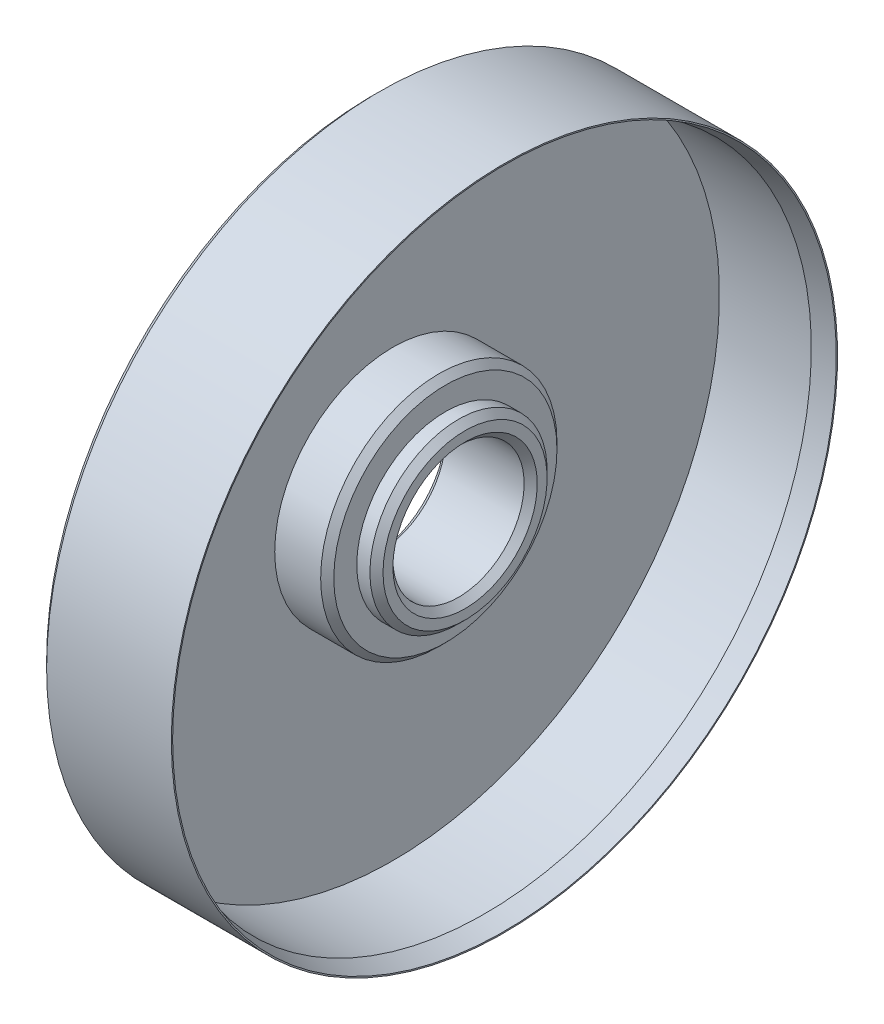
SolidWorks part; units mm, degrees
ref_plane "Спереди" through (0, 0, 0) normal (0, 0, 1) x (1, 0, 0)
ref_plane "Сверху" through (0, 0, 0) normal (0, 1, 0) x (1, 0, 0)
ref_plane "Справа" through (0, 0, 0) normal (1, 0, 0) x (0, 0, -1)
other "Configuration Table"
sketch "Эскиз1" plane through (0, 0, 0) normal (0, 0, 1) x (1, 0, 0)
  line L0 (0, 0) -> (36, 0) construction
  line L1 (0, 11) -> (0, 49.75)
  line L2 (1, 50.75) -> (20, 50.75)
  line L3 (20, 50.75) -> (20, 50.5538)
  line L4 (20, 50.5538) -> (17, 49.75)
  line L5 (17, 49.75) -> (3, 49.75)
  line L6 (3, 49.75) -> (3, 18)
  line L7 (11, 13.5) -> (13, 13.5)
  line L8 (14, 12.5) -> (14, 11)
  line L9 (13, 10) -> (1, 10)
  line L10 (3, 18) -> (10, 18)
  line L11 (11, 17) -> (11, 13.5)
  line L12 (1, 10) -> (0, 11)
  line L13 (14, 11) -> (13, 10)
  line L14 (13, 13.5) -> (14, 12.5)
  line L15 (10, 18) -> (11, 17)
  line L16 (0, 49.75) -> (1, 50.75)
  point P3 (0, 10)
  point P4 (0, 50.75)
  point P11 (14, 13.5)
  point P12 (14, 10)
  point P13 (11, 18)
  dimension "D1" = 20
  dimension "D2" = 14
  dimension "D3" = 3
  dimension "D4" = 27
  dimension "D5" = 8
  dimension "D6" = 36
  dimension "D7" = 20
  dimension "D8" = 15
  dimension "D9" = 1
  dimension "D10" = 101.5
  dimension "D11" = 3
revolve "Повернуть1" add sketch "Эскиз1" angle 360 about L0
